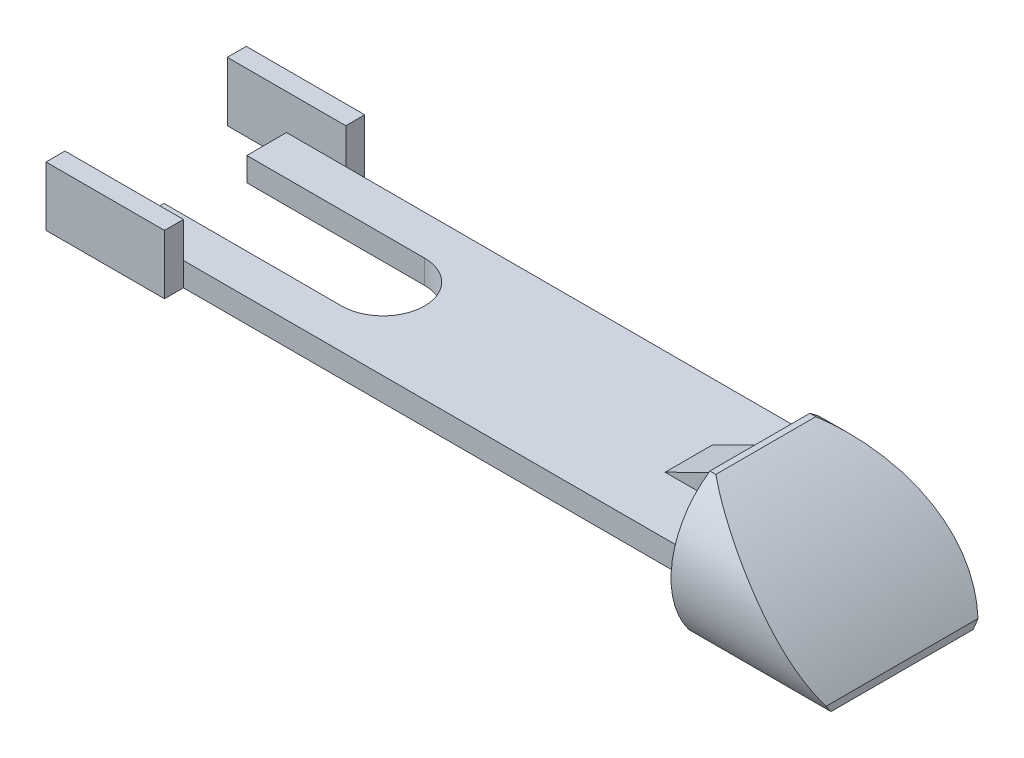
SolidWorks part; units mm, degrees
material "Plain Carbon Steel"
ref_plane "Front Plane" through (0, 0, 0) normal (0, 0, 1) x (1, 0, 0)
ref_plane "Top Plane" through (0, 0, 0) normal (0, 1, 0) x (1, 0, 0)
ref_plane "Right Plane" through (0, 0, 0) normal (1, 0, 0) x (0, 0, -1)
sketch "Sketch1" plane through (0, 0, 0) normal (0, 1, 0) x (1, 0, 0)
  line L1 (-29.718, 8.6995) -> (29.718, 8.6995)
  line L2 (-29.718, 8.6995) -> (-29.718, -8.6995)
  line L3 (-29.718, -8.6995) -> (29.718, -8.6995)
  line L4 (29.718, 8.6995) -> (29.718, -8.6995)
  line L5 (-29.718, 8.6995) -> (29.718, -8.6995) construction
  line L6 (-29.718, -8.6995) -> (29.718, 8.6995) construction
  point P0 (0, 0)
  dimension "D1" = 59.436
  dimension "D2" = 17.399
extrude "Boss-Extrude1" add sketch "Sketch1" along normal blind 2.54
sketch "Sketch2" plane through (0, 2.54, 0) normal (0, 1, 0) x (1, 0, 0)
  line L0 (-29.718, 0) -> (29.718, 0) construction
  line L1 (-29.718, 8.6995) -> (-29.718, -8.6995) construction
  line L2 (29.718, -8.6995) -> (29.718, 8.6995) construction
  line L3 (-29.718, 0) -> (-29.718, 4.445)
  line L4 (-29.718, 0) -> (-29.718, -4.445)
  line L5 (-29.718, 4.445) -> (-10.668, 4.445)
  line L6 (-29.718, -4.445) -> (-10.668, -4.445)
  arc A0 (-10.668, 4.445) -> (-10.668, -4.445) centre (-10.668, 0) cw
  dimension "D1" = 4.445
  dimension "D2" = 4.445
  dimension "D3" = 19.05
extrude "Cut-Extrude1" cut sketch "Sketch2" against normal through all
sketch "Sketch3" plane through (0, 0, 8.6995) normal (0, 0, 1) x (1, 0, 0)
  line L0 (-29.718, 0) -> (29.718, 0) construction
  line L1 (-23.368, 0) -> (-36.068, 0)
  line L2 (-23.368, 0) -> (-23.368, 6.35)
  line L3 (-23.368, 6.35) -> (-36.068, 6.35)
  line L4 (-36.068, 0) -> (-36.068, 6.35)
  point P0 (-29.718, 0)
  dimension "D1" = 12.7
  dimension "D2" = 6.35
  dimension "D3" = 6.35
extrude "Boss-Extrude2" add sketch "Sketch3" along normal blind 2.032
mirror "Mirror1" about plane through (0, 0, 0) normal (0, 0, 1) of "Boss-Extrude2"
sketch "Sketch4" plane through (29.718, 0, 0) normal (1, 0, 0) x (0, 0, -1)
  line L0 (-5.3594, 7.8742) -> (5.3594, 7.8742)
  line L1 (-7.62, -5.715) -> (7.62, -5.715)
  line L2 (10.7315, 0) -> (8.6995, 0) construction
  arc A0 (-5.3594, 7.8742) -> (-7.62, -5.715) centre (0, 0) ccw
  arc A1 (7.62, -5.715) -> (5.3594, 7.8742) centre (0, 0) ccw
  dimension "D1" = 19.05
  dimension "D2" = 10.7188
  dimension "D3" = 15.24
  dimension "D4" = 5.715
extrude "Boss-Extrude3" add sketch "Sketch4" along normal blind 15.24
sketch "Sketch5" plane through (0, 0, 0) normal (0, 0, 1) x (1, 0, 0)
  line L1 (44.958, 7.8742) -> (29.718, 7.8742) construction
  line L2 (44.958, -5.715) -> (44.958, 7.8742) construction
  arc A0 (30.353, 7.8742) -> (44.958, -4.953) centre (13.3453, -26.219) cw
  dimension "D3" = 38.1
  dimension "D1" = 0.635
  dimension "D2" = 0.762
extrude "Cut-Extrude2" cut sketch "Sketch5" against normal through all and the other way through all
sketch "Sketch6" plane through (0, 0, 0) normal (0, 0, 1) x (1, 0, 0)
  line L0 (22.098, 2.54) -> (29.718, 6.3266)
  line L1 (-23.368, 2.54) -> (29.718, 2.54) construction
  line L2 (29.718, 7.8742) -> (29.718, -5.715) construction
  dimension "D1" = 8.509
  dimension "D2" = 7.62
rib "Rib1" sketch "Sketch6" sketch "Sketch6" thickness 5.08 extrusion direction parallel to sketch draft on no parameters "D1"=5.08
ref_plane "Plane4" through (0, 5.08, 0) normal (0, 1, 0) x (1, 0, 0)
